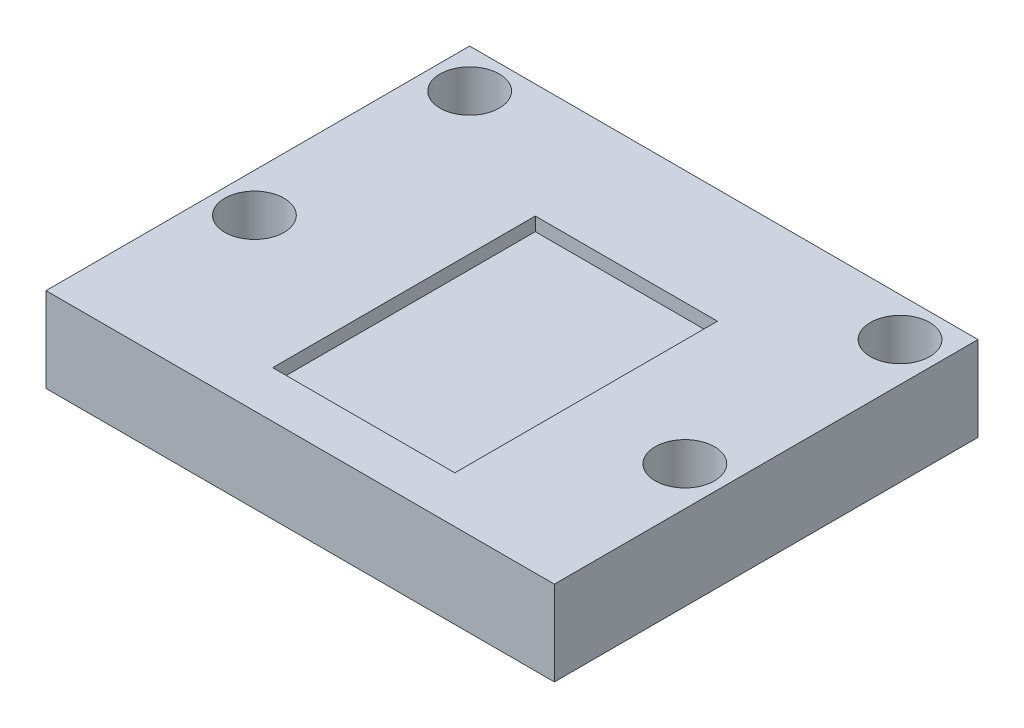
SolidWorks part; units mm, degrees
ref_plane "Front Plane" through (0, 0, 0) normal (0, 0, 1) x (1, 0, 0)
ref_plane "Top Plane" through (0, 0, 0) normal (0, 1, 0) x (1, 0, 0)
ref_plane "Right Plane" through (0, 0, 0) normal (1, 0, 0) x (0, 0, -1)
sketch "Sketch2" plane through (0, 0, 0) normal (0, 1, 0) x (1, 0, 0)
  line L1 (0, 0) -> (60, 0)
  line L2 (0, 0) -> (0, 50)
  line L3 (0, 50) -> (60, 50)
  line L4 (60, 0) -> (60, 50)
  dimension "D1" = 50
  dimension "D2" = 60
extrude "Boss-Extrude1" add sketch "Sketch2" along normal blind 10
sketch "Sketch1" plane through (0, 10, 0) normal (0, 1, 0) x (1, 0, 0)
  line L0 (60, 50) -> (0, 50) construction
  line L5 (4.6, 45.4) -> (55.4, 45.4) construction
  line L6 (4.6, 45.4) -> (4.6, 20) construction
  line L7 (4.6, 20) -> (55.4, 20) construction
  line L8 (55.4, 45.4) -> (55.4, 20) construction
  line L10 (4.6, 45.4) -> (0, 45.4)
  line L11 (0, 50) -> (0, 0) construction
  line L12 (4.6, 45.4) -> (4.6, 50)
  circle A0 centre (4.6, 20) radius 3.5
  circle A1 centre (4.6, 45.4) radius 3.5
  circle A2 centre (55.4, 45.4) radius 3.5
  circle A3 centre (55.4, 20) radius 3.5
  point P2 (30, 50)
  point P3 (30, 45.4)
  dimension "D5" = 7
  dimension "D3" = 25.4
  dimension "D4" = 50.8
extrude "Cut-Extrude1" cut sketch "Sketch1" against normal blind 10 contours L12 A1 L10 | L10 A1 L12 | A2 | A0 | A3
sketch "Sketch3" plane through (0, 10, 0) normal (0, 1, 0) x (1, 0, 0)
  line L0 (60, 50) -> (0, 50) construction
  line L1 (21.25, 36.5) -> (42.75, 36.5)
  line L2 (21.25, 36.5) -> (21.25, 5.5)
  line L3 (21.25, 5.5) -> (42.75, 5.5)
  line L4 (42.75, 36.5) -> (42.75, 5.5)
  circle A0 centre (30, 32.5) radius 2.25 construction
  point P6 (0, 0)
  point P9 (30, 50)
  dimension "D4" = 4.5
  dimension "D1" = 21.5
  dimension "D2" = 31
  dimension "D3" = 4
  dimension "D5" = 8.75
  dimension "D6" = 17.5
extrude "Cut-Extrude2" cut sketch "Sketch3" against normal blind 1.6
